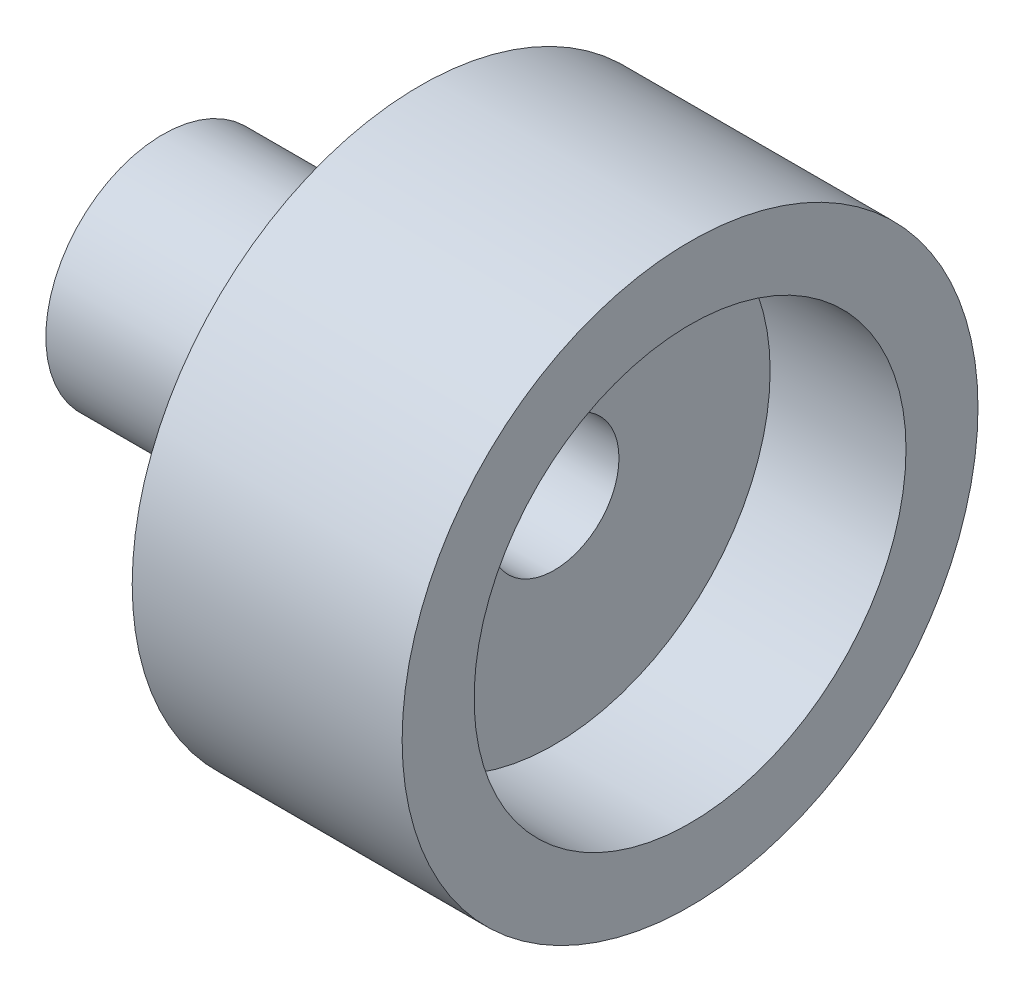
SolidWorks part; units mm, degrees
material "ABS PC"
ref_plane "Front Plane" through (0, 0, 0) normal (0, 0, 1) x (1, 0, 0)
ref_plane "Top Plane" through (0, 0, 0) normal (0, 1, 0) x (1, 0, 0)
ref_plane "Right Plane" through (0, 0, 0) normal (1, 0, 0) x (0, 0, -1)
sketch "Sketch2" plane through (0, 0, 0) normal (1, 0, 0) x (0, 0, -1)
  circle A0 centre (0, 0) radius 8
  circle A1 centre (0, 0) radius 3.25
  dimension "D1" = 16
extrude "Boss-Extrude1" add sketch "Sketch2" along normal blind 7.5
sketch "Sketch3" plane through (7.5, 0, 0) normal (1, 0, 0) x (0, 0, -1)
  circle A0 centre (0, 0) radius 6
extrude "Cut-Extrude1" cut sketch "Sketch3" against normal blind 3.775
sketch "Sketch4" plane through (3.725, 0, 0) normal (1, 0, 0) x (0, 0, -1)
  circle A0 centre (0, 0) radius 1.8
  circle A1 centre (0, 0) radius 3.25
extrude "Boss-Extrude2" add sketch "Sketch4" against normal blind 10.875
